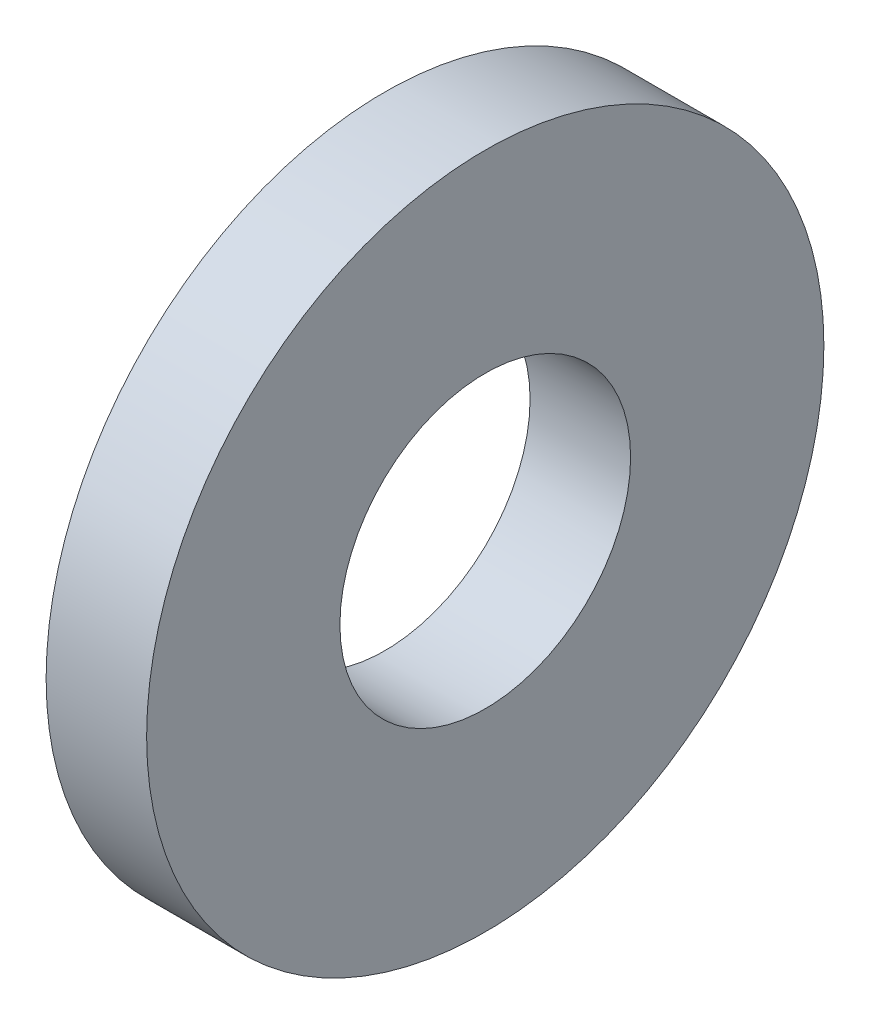
SolidWorks part; units mm, degrees
material "Plain Carbon Steel"
ref_plane "Front Plane" through (0, 0, 0) normal (0, 0, 1) x (1, 0, 0)
ref_plane "Top Plane" through (0, 0, 0) normal (0, 1, 0) x (1, 0, 0)
ref_plane "Right Plane" through (0, 0, 0) normal (1, 0, 0) x (0, 0, -1)
sketch "Sketch1" plane through (0, 0, 0) normal (1, 0, 0) x (0, 0, -1)
  circle A0 centre (0, 0) radius 5.5626
  circle A1 centre (0, 0) radius 2.3876
  dimension "OD" = 11.1252
  dimension "ID" = 4.7752
extrude "Boss-Extrude1" add sketch "Sketch1" along normal blind 1.651
